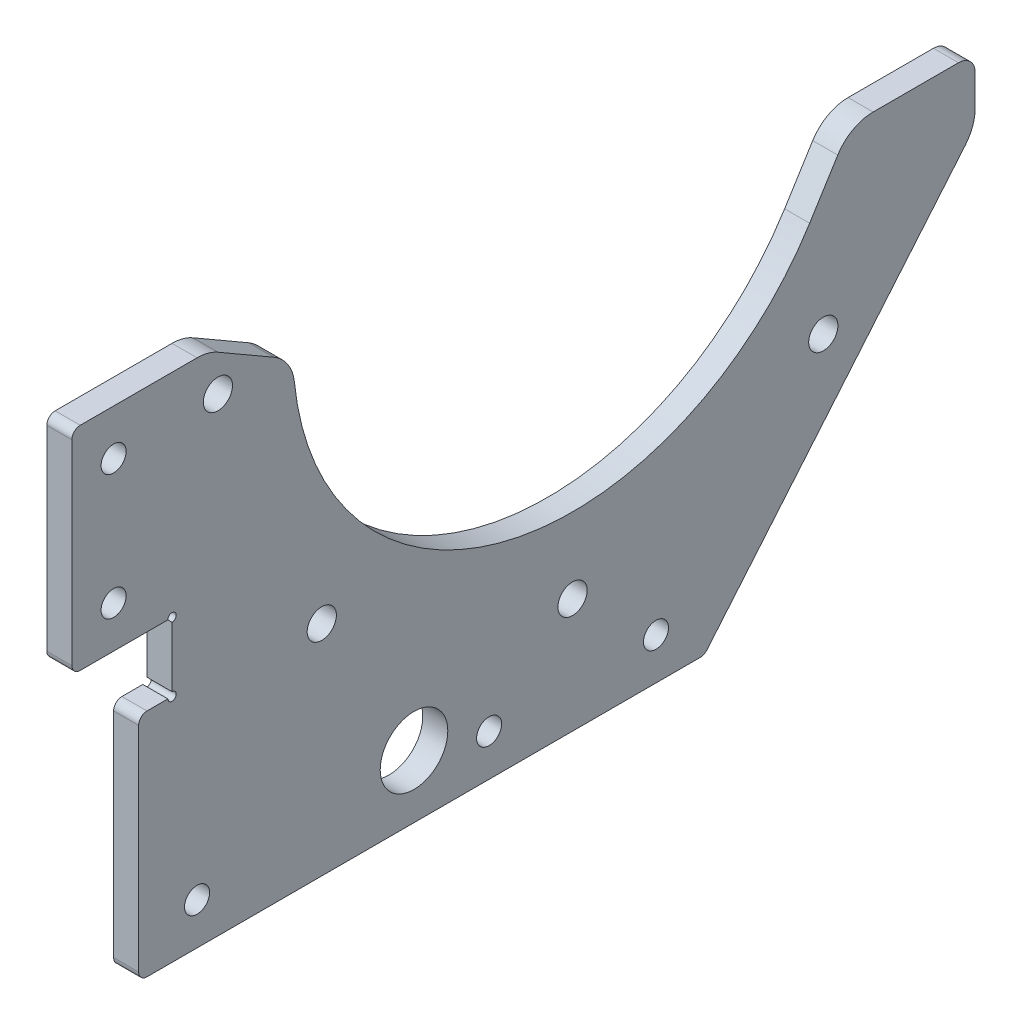
SolidWorks part; units mm, degrees
material "环氧板3240"
ref_plane "前视基准面" through (0, 0, 0) normal (0, 0, 1) x (1, 0, 0)
ref_plane "上视基准面" through (0, 0, 0) normal (0, 1, 0) x (1, 0, 0)
ref_plane "右视基准面" through (0, 0, 0) normal (1, 0, 0) x (0, 0, -1)
other "Configuration Table"
sketch "草图1" plane through (0, 0, 0) normal (1, 0, 0) x (0, 0, -1)
  line L1 (-48, -28.65) -> (-60, -28.65)
  line L2 (-48, -28.65) -> (-48, -20.45)
  line L3 (0, 0) -> (30.052, -30.052) construction
  line L4 (0, 0) -> (0, -42.5) construction
  line L5 (33.25, -10) -> (48.25, -10)
  line L9 (42.5, 0) -> (-42.5, 0) construction
  line L10 (0, -42.5) -> (0, -56.25) construction
  line L11 (13.7477, -46.25) -> (-13.7477, -46.25) construction
  line L12 (-43.6603, 5) -> (-60, 5)
  line L13 (-60, 5) -> (-60, -20.45)
  line L15 (-60, -56.25) -> (15.7865, -56.25)
  line L20 (-13.7477, 46.25) -> (13.7477, 46.25) construction
  line L21 (-48, -20.45) -> (-60, -20.45)
  line L23 (-60, -20.45) -> (-60, -56.25) construction
  line L26 (48.25, -17.5616) -> (15.7865, -56.25)
  line L27 (48.25, -17.5616) -> (48.25, -10)
  line L28 (19.982, -51.25) -> (-60, -51.25) construction
  line L36 (-52, -28.65) -> (-52, -56.25)
  line L37 (28.4158, -17.7423) -> (33.25, -10)
  line L38 (-55, -15.45) -> (-55, 5) construction
  line L39 (-43.6603, 5) -> (-33.4886, -0.8726)
  line L40 (-43.6603, 5) -> (47.9902, 5) construction
  line L41 (0, 0) -> (-59.242, 34.2034) construction
  line L42 (-16.2321, 29.5789) -> (-50.492, 49.3589) construction
  line L43 (-16.2321, 29.5789) -> (-33.7321, -0.732) construction
  line L44 (-50.492, 49.3589) -> (-67.992, 19.048) construction
  line L45 (-33.7321, -0.732) -> (-67.992, 19.048) construction
  arc A0 (-33.4886, -0.8726) -> (28.4158, -17.7423) centre (0, 0) ccw
  circle A1 centre (0, 0) radius 42.5 construction
  circle A2 centre (0, -42.5) radius 1.75
  circle A3 centre (30.052, -30.052) radius 1.75
  circle A4 centre (-30.052, -30.052) radius 1.75
  circle A6 centre (-10, -51.25) radius 1.5
  circle A7 centre (0, 0) radius 48.25 construction
  circle A8 centre (10, -51.25) radius 1.5
  circle A10 centre (-42.5, 0) radius 1.75
  circle A14 centre (-45, -51.25) radius 1.5
  circle A15 centre (-55, -15.45) radius 1.5
  circle A16 centre (-55, -15.45) radius 3.5 construction
  circle A17 centre (-55, -0.45) radius 1.5
  point P49 (-39.5589, 22.8393)
  point P59 (-59.242, 34.2034)
  dimension "D1" = 67
  dimension "D6" = 3.5
  dimension "D7" = 85
  dimension "D3" = 92.5
  dimension "D8" = 20
  dimension "D9" = 96.5
  dimension "D12" = 3
  dimension "D13" = 60
  dimension "D22" = 7
  dimension "D23" = 5
  dimension "D14" = 35
  dimension "D21" = 7
  dimension "D26" = 5
  dimension "D29" = 15
  dimension "D2" = 45
  dimension "D4" = 10
  dimension "D5" = 10
  dimension "D10" = 5
  dimension "D15" = 15
  dimension "D16" = 5
  dimension "D17" = 27.6
  dimension "D18" = 8.2
  dimension "D19" = 12
  dimension "D20" = 8
  dimension "D24" = 35
  dimension "D25" = 50
  dimension "D27" = 10
  dimension "D28" = 30
  dimension "D30" = 30
extrude "凸台-拉伸1" add sketch "草图1" along normal blind 3
fillet "圆角1" radius 5 4 edges at (1.5, 5, 43.6603) (1.5, -0.8726, 33.4886) (1.5, -10, -33.25) (1.5, -17.5616, -48.25)
sketch "草图2" plane through (0, 0, 0) normal (-1, 0, 0) x (0, 0, 1)
  circle A0 centre (48, -20.45) radius 0.5
  circle A1 centre (48, -28.65) radius 0.5
  dimension "D1" = 1
extrude "切除-拉伸1" cut sketch "草图2" against normal blind 10
fillet "圆角2" radius 2 1 edges at (1.5, -10, -48.25)
sketch "草图3" plane through (0, 0, 0) normal (-1, 0, 0) x (0, 0, 1)
  line L0 (52, -56.25) -> (-15.7865, -56.25) construction
  line L1 (52, -28.65) -> (52, -56.25) construction
  circle A0 centre (19, -48.75) radius 4.05
  dimension "D1" = 8.1
  dimension "D3" = 33
  dimension "D2" = 7.5
extrude "切除-拉伸2" cut sketch "草图3" against normal blind 10
fillet "圆角3" radius 1 5 edges at (1.5, 5, 60) (1.5, -20.45, 60) (1.5, -28.65, 52) (1.5, -56.25, 52) (1.5, -56.25, -15.7865)
